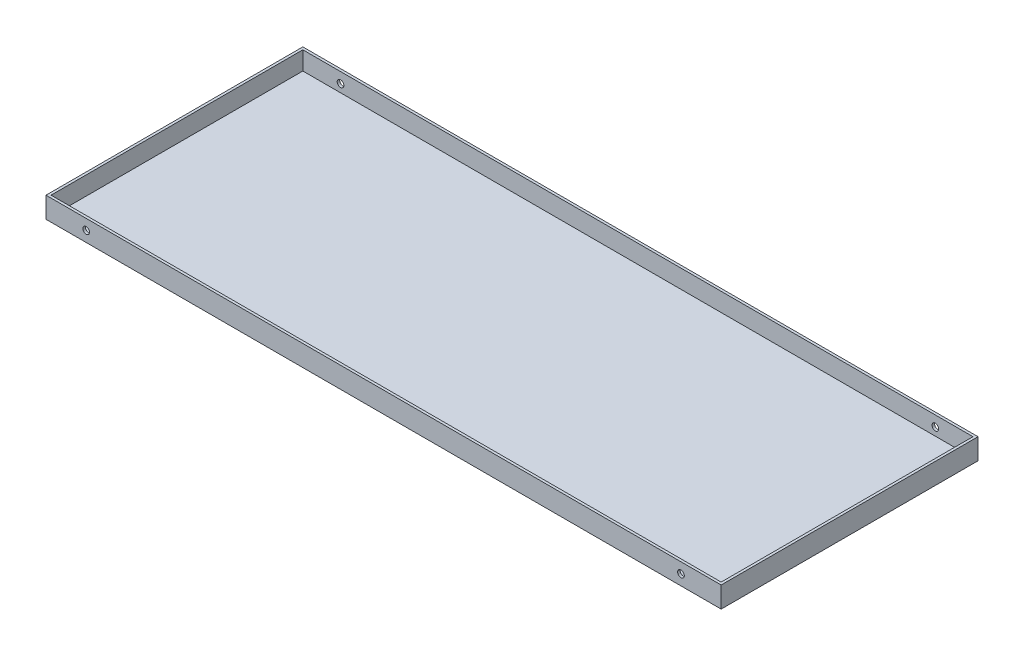
SolidWorks part; units mm, degrees
ref_plane "前基準面" through (0, 0, 0) normal (0, 0, 1) x (1, 0, 0)
ref_plane "上基準面" through (0, 0, 0) normal (0, 1, 0) x (1, 0, 0)
ref_plane "右基準面" through (0, 0, 0) normal (1, 0, 0) x (0, 0, -1)
sketch "草圖2" plane through (0, 0, 0) normal (0, 1, 0) x (1, 0, 0)
  line L0 (0, 0) -> (0, -307)
  line L1 (0, -307) -> (807, -307)
  line L2 (807, -307) -> (807, 0)
  line L3 (807, 0) -> (0, 0)
  dimension "D1" = 807
  dimension "D2" = 307
extrude "填料-伸長1" add sketch "草圖2" along normal blind 25
sketch "草圖3" plane through (0, 25, 0) normal (0, 1, 0) x (1, 0, 0)
  line L14 (804, -304) -> (804, -3)
  line L15 (3, -304) -> (804, -304)
  line L16 (3, -3) -> (3, -304)
  line L17 (804, -3) -> (3, -3)
  line L18 (804, -304) -> (804, -3)
  line L19 (3, -304) -> (804, -304)
  line L20 (3, -3) -> (3, -304)
  line L21 (804, -3) -> (3, -3)
  dimension "D1" = 3
extrude "除料-伸長1" cut sketch "草圖3" against normal blind 22
sketch "草圖4" plane through (0, 0, 307) normal (0, 0, 1) x (1, 0, 0)
  line L0 (807, 25) -> (807, 0) construction
  line L1 (0, 25) -> (807, 25) construction
  line L2 (0, 25) -> (0, 0) construction
  circle A0 centre (759, 12.5) radius 4
  circle A1 centre (48, 12.5) radius 4
  dimension "D1" = 8
  dimension "D4" = 8
  dimension "D2" = 48
  dimension "D3" = 12.5
  dimension "D5" = 48
  dimension "D6" = 12.5
extrude "除料-伸長2" cut sketch "草圖4" against normal through all
